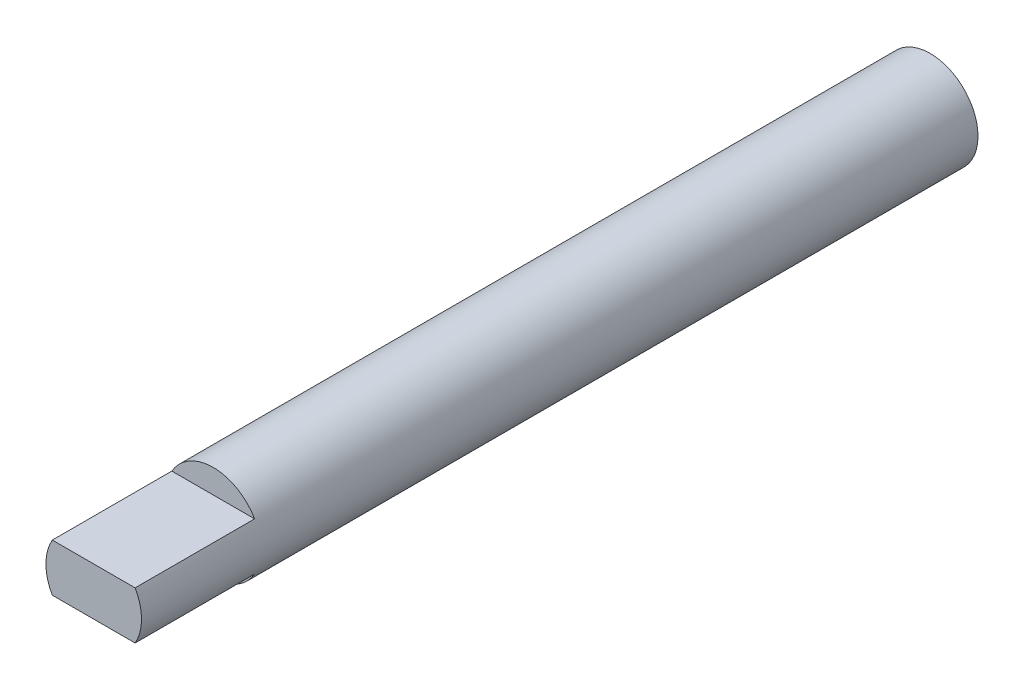
SolidWorks part; units mm, degrees
ref_plane "Front Plane" through (0, 0, 0) normal (0, 0, 1) x (1, 0, 0)
ref_plane "Top Plane" through (0, 0, 0) normal (0, 1, 0) x (1, 0, 0)
ref_plane "Right Plane" through (0, 0, 0) normal (1, 0, 0) x (0, 0, -1)
sketch "Sketch1" plane through (0, 0, 0) normal (0, 0, 1) x (1, 0, 0)
  circle A0 centre (0, 0) radius 4
  dimension "D1" = 8
extrude "Boss-Extrude1" add sketch "Sketch1" along normal mid plane 70
sketch "Sketch2" plane through (0, 0, 35) normal (0, 0, 1) x (1, 0, 0)
  line L0 (-4, 0) -> (4, 0) construction
  line L1 (-4, -2) -> (4, -2)
  line L2 (-4, 2) -> (4, 2)
  line L3 (-4, 2) -> (-4, 4.53)
  line L4 (-4, 4.53) -> (4, 4.53)
  line L5 (4, 4.53) -> (4, 2)
  line L6 (4, -2) -> (4, -4.562)
  line L7 (4, -4.562) -> (-4, -4.7114)
  line L8 (-4, -4.7114) -> (-4, -2)
  circle A0 centre (0, 0) radius 4 construction
  dimension "D1" = 2
  dimension "D2" = 2
extrude "Cut-Extrude1" cut sketch "Sketch2" against normal blind 10
